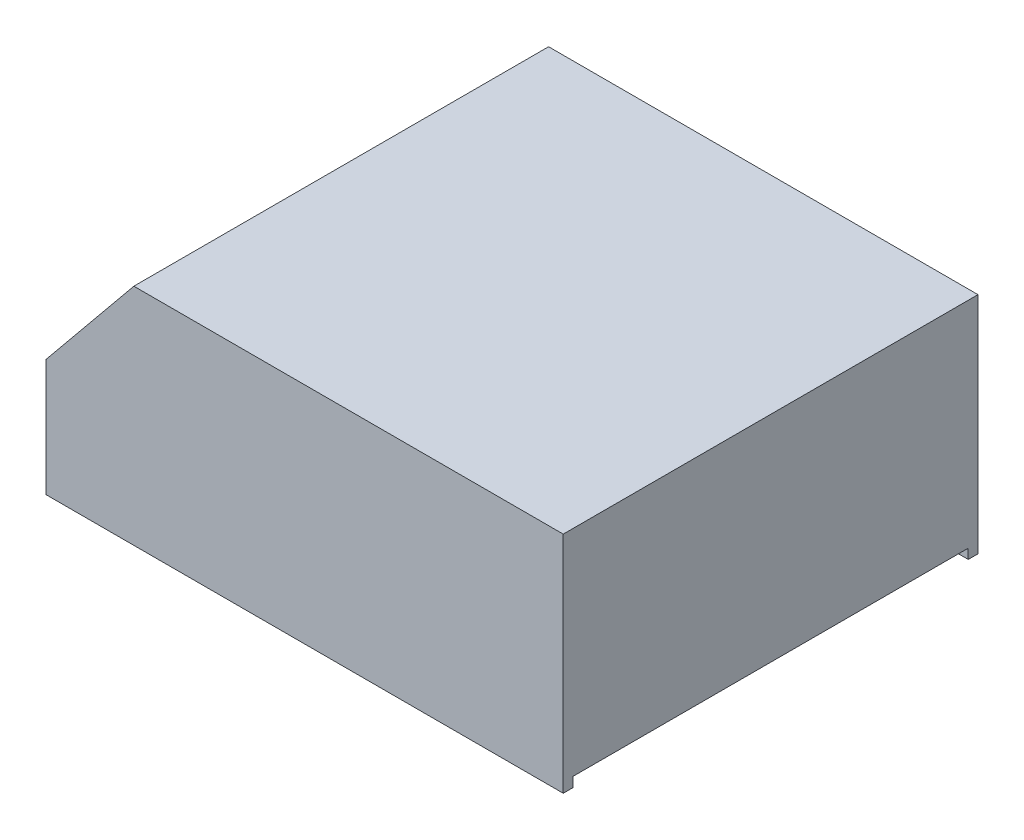
SolidWorks part; units mm, degrees
ref_plane "Alzado" through (0, 0, 0) normal (0, 0, 1) x (1, 0, 0)
ref_plane "Planta" through (0, 0, 0) normal (0, 1, 0) x (1, 0, 0)
ref_plane "Vista lateral" through (0, 0, 0) normal (1, 0, 0) x (0, 0, -1)
sketch "Croquis2" plane through (0, 0, 0) normal (0, 0, 1) x (1, 0, 0)
  line L0 (0, 0) -> (0, 46)
  line L1 (0, 46) -> (-88, 46)
  line L2 (-88, 46) -> (-106, 24)
  line L3 (-106, 24) -> (-106, 0)
  line L4 (-106, 0) -> (0, 0)
  line L5 (-88, 46) -> (-88, 0) construction
  dimension "D1" = 46
  dimension "D2" = 22
  dimension "D3" = 18
  dimension "D4" = 88
extrude "Saliente-Extruir1" add sketch "Croquis2" along normal blind 85
sketch "Croquis3" plane through (0, 0, 0) normal (0, -1, 0) x (1, 0, 0)
  line L0 (-106, 85) -> (-106, 0) construction
  line L1 (-88, 55.5) -> (-106, 55.5)
  line L2 (-88, 55.5) -> (-88, 29.5)
  line L3 (-88, 29.5) -> (-106, 29.5)
  line L4 (-106, 55.5) -> (-106, 29.5)
  line L5 (-88, 55.5) -> (-106, 29.5) construction
  line L6 (-88, 29.5) -> (-106, 55.5) construction
  line L9 (-88, 85) -> (-88, 0) construction
  line L10 (-106, 0) -> (0, 0) construction
  point P0 (-97, 42.5)
  dimension "D1" = 26
  dimension "D2" = 42.5
extrude "Cortar-Extruir1" cut sketch "Croquis3" against normal through all
shell "Vaciado1" thickness 2
sketch "Croquis4" plane through (0, 0, 0) normal (0, -1, 0) x (1, 0, 0)
  line L0 (-104, 27.5) -> (-87.0522, 27.5) construction
  line L1 (-104, 83) -> (-2, 83) construction
  line L2 (-104, 83) -> (-104, 57.5) construction
  line L3 (-104, 27.5) -> (-104, 2) construction
  circle A0 centre (-95, 69.6) radius 4
  circle A1 centre (-95, 14.1) radius 4
  point P4 (-96.0325, 13.722)
  dimension "D1" = 8
  dimension "D2" = 8
  dimension "D3" = 13.4
  dimension "D4" = 13.4
  dimension "D5" = 9
  dimension "D6" = 9
extrude "Saliente-Extruir2" add sketch "Croquis4" against normal up to next
sketch "Croquis5" plane through (0, 0, 0) normal (0, -1, 0) x (1, 0, 0)
  circle A0 centre (-95, 69.6) radius 4 construction
  circle A1 centre (-95, 14.1) radius 4 construction
  circle A2 centre (-95, 69.6) radius 4
  circle A3 centre (-95, 14.1) radius 4
extrude "Cortar-Extruir2" cut sketch "Croquis5" against normal blind 2
sketch "Croquis8" plane through (0, 0, 0) normal (0, -1, 0) x (1, 0, 0)
  line L0 (0, 85) -> (0, 0) construction
  line L1 (-2, 83) -> (0, 83)
  line L2 (-2, 83) -> (-2, 2)
  line L3 (-2, 2) -> (0, 2)
  line L4 (0, 83) -> (0, 2)
extrude "Cortar-Extruir3" cut sketch "Croquis8" against normal blind 2
sketch "Croquis9" plane through (0, 2, 0) normal (0, -1, 0) x (1, 0, 0)
  circle A0 centre (-95, 69.6) radius 1.5
  circle A1 centre (-95, 14.1) radius 1.5
  dimension "D1" = 3
  dimension "D2" = 3
extrude "Cortar-Extruir4" cut sketch "Croquis9" against normal blind 10
